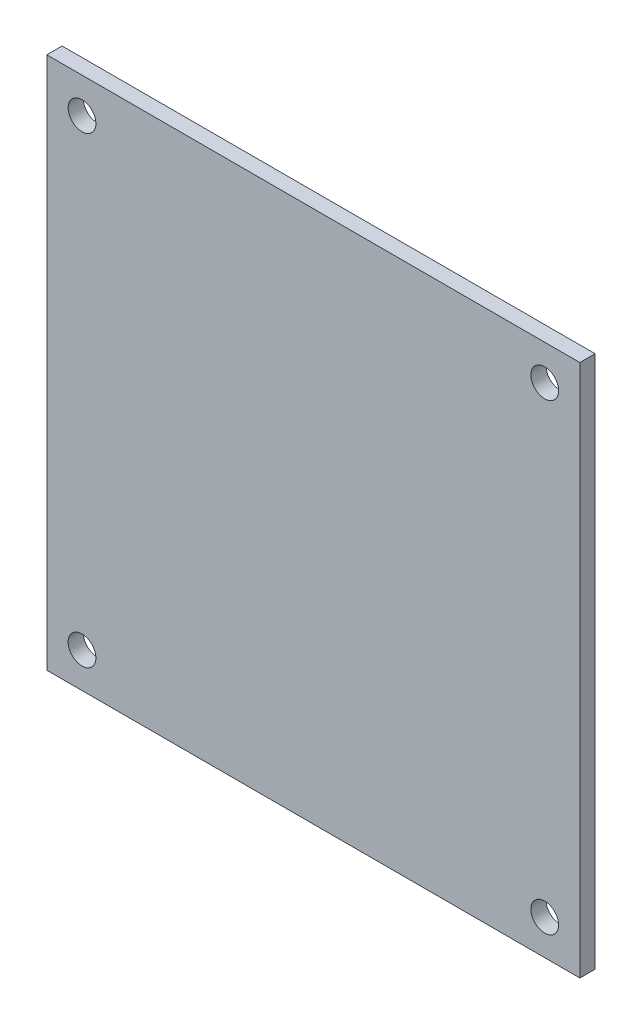
SolidWorks part; units mm, degrees
ref_plane "前视基准面" through (0, 0, 0) normal (0, 0, 1) x (1, 0, 0)
ref_plane "上视基准面" through (0, 0, 0) normal (0, 1, 0) x (1, 0, 0)
ref_plane "右视基准面" through (0, 0, 0) normal (1, 0, 0) x (0, 0, -1)
sketch "草图1" plane through (0, 0, 0) normal (0, 0, 1) x (1, 0, 0)
  line L1 (-28.7977, 28.7977) -> (28.7977, 28.7977)
  line L2 (-28.7977, 28.7977) -> (-28.7977, -28.7977)
  line L3 (-28.7977, -28.7977) -> (28.7977, -28.7977)
  line L4 (28.7977, 28.7977) -> (28.7977, -28.7977)
  line L5 (-28.7977, 28.7977) -> (28.7977, -28.7977) construction
  line L6 (-28.7977, -28.7977) -> (28.7977, 28.7977) construction
  line L7 (-25, 25) -> (25, 25) construction
  line L8 (-25, 25) -> (-25, -25) construction
  line L9 (-25, -25) -> (25, -25) construction
  line L10 (25, 25) -> (25, -25) construction
  line L11 (-25, 25) -> (25, -25) construction
  line L12 (-25, -25) -> (25, 25) construction
  circle A0 centre (-25, 25) radius 1.5
  circle A1 centre (25, 25) radius 1.5
  circle A2 centre (-25, -25) radius 1.5
  circle A3 centre (25, -25) radius 1.5
  point P0 (0, 0)
  point P5 (0, 0)
extrude "凸台-拉伸1" add sketch "草图1" along normal blind 1.65
